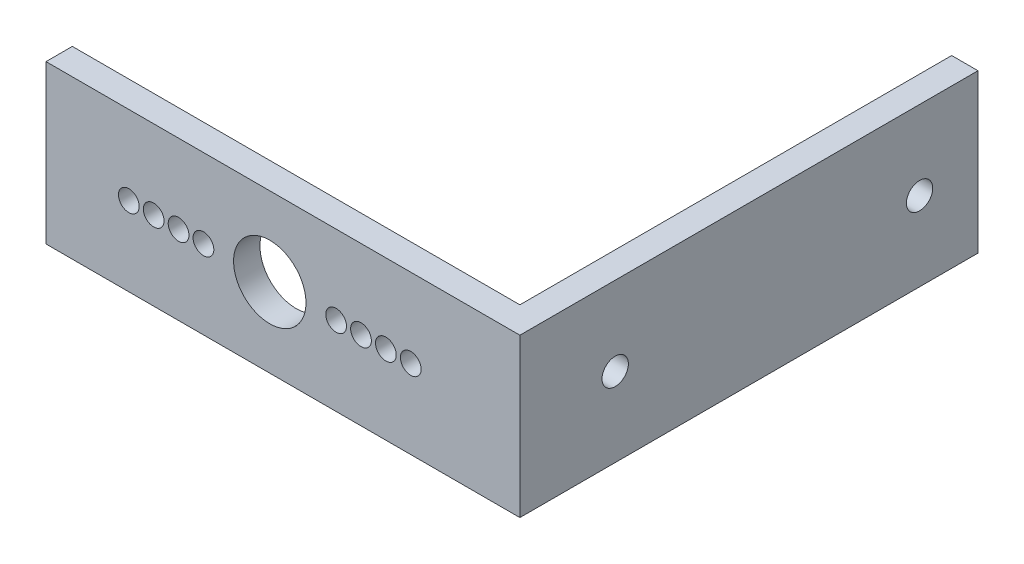
SolidWorks part; units mm, degrees
ref_plane "Front" through (0, 0, 0) normal (0, 0, 1) x (1, 0, 0)
ref_plane "Top" through (0, 0, 0) normal (0, 1, 0) x (1, 0, 0)
ref_plane "Right" through (0, 0, 0) normal (1, 0, 0) x (0, 0, -1)
sketch "Sketch1" plane through (0, 0, 0) normal (0, 0, 1) x (1, 0, 0)
  line L0 (26.9875, 19.05) -> (26.9875, 0) construction
  line L1 (0, 0) -> (53.975, 0)
  line L2 (0, 0) -> (0, 19.05)
  line L3 (0, 19.05) -> (53.975, 19.05)
  line L4 (53.975, 0) -> (53.975, 19.05)
  line L5 (0, 9.525) -> (53.975, 9.525) construction
  circle A0 centre (34.9875, 9.525) radius 1.25
  circle A1 centre (43.9875, 9.525) radius 1.25
  circle A2 centre (37.9875, 9.525) radius 1.25
  circle A3 centre (40.9875, 9.525) radius 1.25
  circle A4 centre (18.9875, 9.525) radius 1.25
  circle A5 centre (15.9875, 9.525) radius 1.25
  circle A6 centre (12.9875, 9.525) radius 1.25
  circle A7 centre (9.9875, 9.525) radius 1.25
  circle A8 centre (26.9875, 9.525) radius 4.3656
  point P19 (26.9875, 9.525)
  point P28 (0, 0)
  point P29 (17.7361, 13.71)
  point P44 (26.9875, 9.525)
  dimension "D7" = 2.5
  dimension "D9" = 8.7312
  dimension "D1" = 53.975
  dimension "D2" = 19.05
  dimension "D3" = 8
  dimension "D4" = 11
  dimension "D5" = 14
  dimension "D6" = 17
  dimension "D8" = 2
extrude "Boss-Extrude1" add sketch "Sketch1" along normal blind 3.175
sketch "Sketch2" plane through (53.975, 0, 0) normal (1, 0, 0) x (0, 0, -1)
  line L0 (-3.175, 19.05) -> (0, 19.05) construction
  line L1 (-3.175, 0) -> (52.07, 0)
  line L2 (-3.175, 0) -> (-3.175, 19.05)
  line L3 (-3.175, 19.05) -> (52.07, 19.05)
  line L4 (52.07, 0) -> (52.07, 19.05)
  line L5 (8.3185, 9.525) -> (45.0215, 9.525) construction
  circle A0 centre (8.3185, 9.525) radius 1.5875
  circle A1 centre (45.0215, 9.525) radius 1.5875
  point P7 (26.67, 9.525)
  point P8 (52.07, 9.525)
  dimension "D3" = 3.175
  dimension "D1" = 55.245
  dimension "D2" = 36.703
  dimension "D4" = 25.4
extrude "Boss-Extrude2" add sketch "Sketch2" along normal blind 3.175
